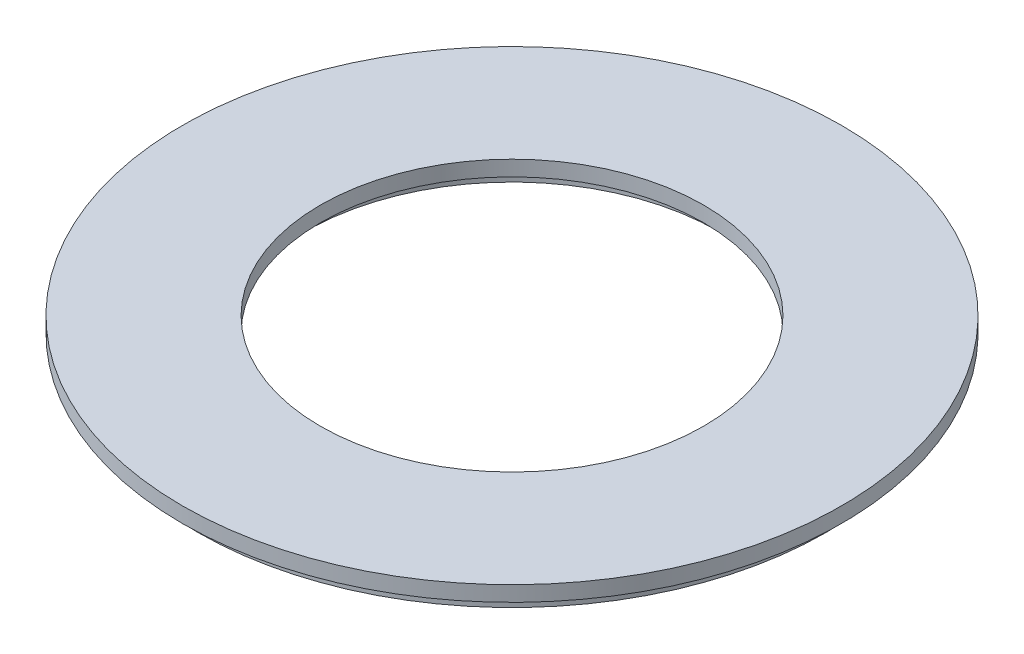
SolidWorks part; units mm, degrees
ref_plane "Front Plane" through (0, 0, 0) normal (0, 0, 1) x (1, 0, 0)
ref_plane "Top Plane" through (0, 0, 0) normal (0, 1, 0) x (1, 0, 0)
ref_plane "Right Plane" through (0, 0, 0) normal (1, 0, 0) x (0, 0, -1)
sketch "Sketch1" plane through (0, 0, 0) normal (0, 1, 0) x (1, 0, 0)
  circle A0 centre (0, 0) radius 12.5
  circle A1 centre (0, 0) radius 21.5
extrude "Boss-Extrude1" add sketch "Sketch1" along normal blind 1
sketch "Sketch2" plane through (0, 0, 0) normal (0, -1, 0) x (1, 0, 0)
  circle A0 centre (0, 0) radius 20.5
  circle A1 centre (0, 0) radius 13.5
  circle A2 centre (0, 0) radius 12.5 construction
  circle A3 centre (0, 0) radius 21.5 construction
  dimension "D1" = 1
  dimension "D2" = 1
extrude "Boss-Extrude2" add sketch "Sketch2" along normal blind 1
